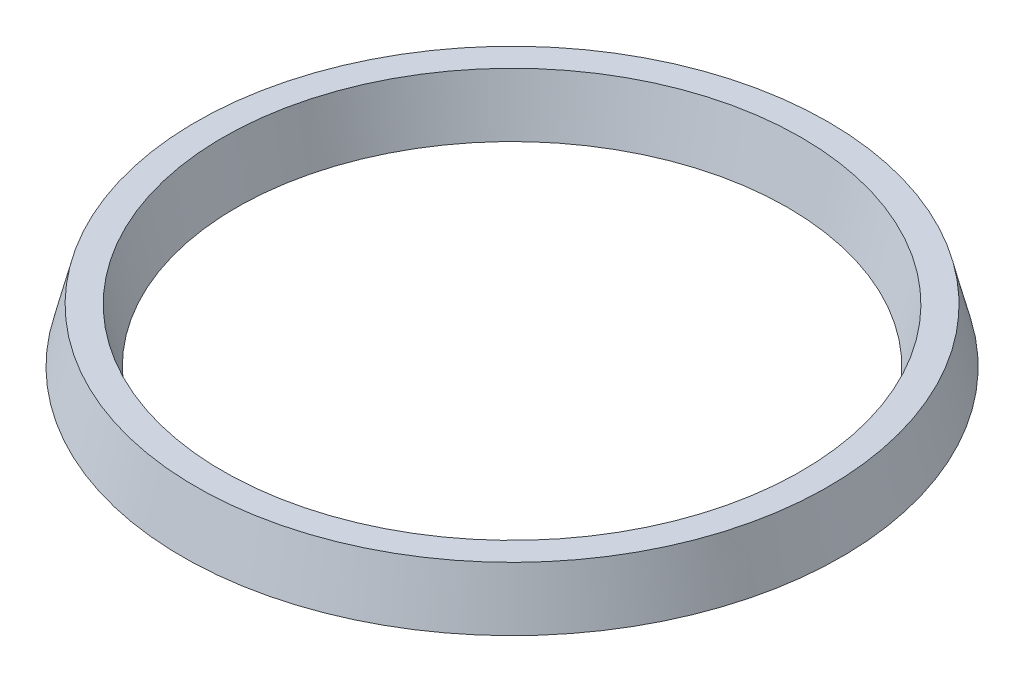
SolidWorks part; units mm, degrees
ref_plane "Front Plane" through (0, 0, 0) normal (0, 0, 1) x (1, 0, 0)
ref_plane "Top Plane" through (0, 0, 0) normal (0, 1, 0) x (1, 0, 0)
ref_plane "Right Plane" through (0, 0, 0) normal (1, 0, 0) x (0, 0, -1)
sketch "Sketch1" plane through (0, 0, 0) normal (0, 0, 1) x (1, 0, 0)
  line L0 (0, 20.2906) -> (0, 0) construction
  line L1 (0, 0) -> (-67.31, 0) construction
  line L2 (-67.31, 0) -> (-67.31, 22.7143) construction
  line L3 (3, 6) -> (-3, 6)
  line L4 (-3, 6) -> (-6, -6)
  line L5 (-6, -6) -> (-3, -6)
  line L6 (-3, -6) -> (-1.8638, -1.4552)
  line L7 (1.8638, -1.4552) -> (3, -6)
  line L8 (3, -6) -> (6, -6)
  line L9 (6, -6) -> (3, 6)
  arc A1 (-1.8638, -1.4552) -> (1.8638, -1.4552) centre (0, -1.9212) cw
  dimension "D8" = 67.31
  dimension "D1" = 6
  dimension "D2" = 12
  dimension "D3" = 3
  dimension "D4" = 12
  dimension "D5" = 6
  dimension "D6" = 6
  dimension "D7" = 3
revolve "Revolve1" add sketch "Sketch1" angle 360 about L2
